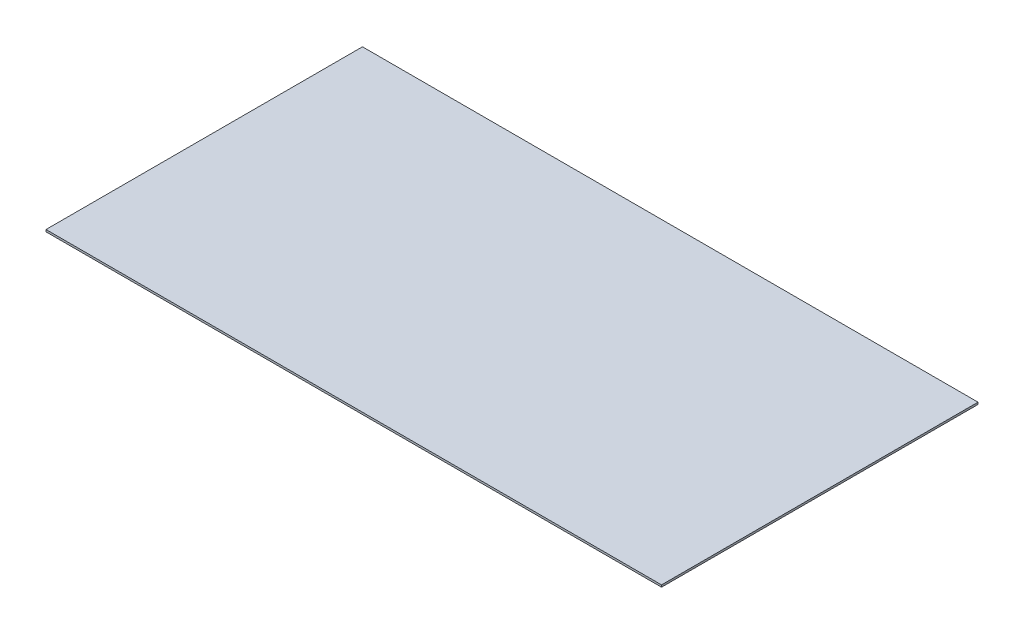
SolidWorks part; units mm, degrees
ref_plane "Front Plane" through (0, 0, 0) normal (0, 0, 1) x (1, 0, 0)
ref_plane "Top Plane" through (0, 0, 0) normal (0, 1, 0) x (1, 0, 0)
ref_plane "Right Plane" through (0, 0, 0) normal (1, 0, 0) x (0, 0, -1)
sketch "Sketch1" plane through (0, 0, 0) normal (0, 1, 0) x (1, 0, 0)
  line L1 (-151.593, -77.9362) -> (151.593, -77.9362)
  line L2 (-151.593, -77.9362) -> (-151.593, 77.9362)
  line L3 (-151.593, 77.9362) -> (151.593, 77.9362)
  line L4 (151.593, -77.9362) -> (151.593, 77.9362)
  line L5 (-151.593, -77.9362) -> (151.593, 77.9362) construction
  line L6 (-151.593, 77.9362) -> (151.593, -77.9362) construction
  point P0 (0, 0)
extrude "Boss-Extrude1" add sketch "Sketch1" along normal blind 1
equation "\"`1\"=10"
